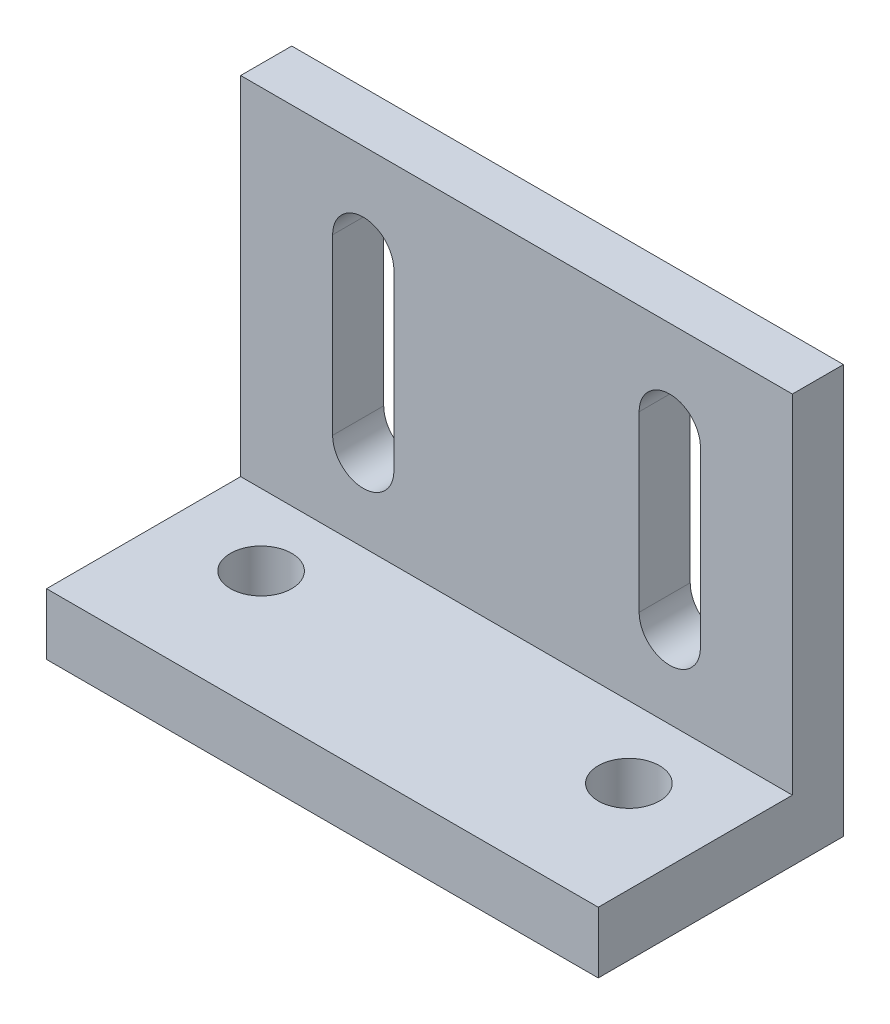
SolidWorks part; units mm, degrees
ref_plane "Front Plane" through (0, 0, 0) normal (0, 0, 1) x (1, 0, 0)
ref_plane "Top Plane" through (0, 0, 0) normal (0, 1, 0) x (1, 0, 0)
ref_plane "Right Plane" through (0, 0, 0) normal (1, 0, 0) x (0, 0, -1)
sketch "Sketch1" plane through (0, 0, 0) normal (1, 0, 0) x (0, 0, -1)
  line L0 (0, 0) -> (-12, 0)
  line L1 (-12, 0) -> (-12, 3)
  line L2 (-12, 3) -> (-2.5, 3)
  line L3 (-2.5, 3) -> (-2.5, 20)
  line L4 (-2.5, 20) -> (0, 20)
  line L5 (0, 20) -> (0, 0)
  dimension "D1" = 12
  dimension "D2" = 3
  dimension "D3" = 2.5
  dimension "D4" = 20
extrude "Boss-Extrude1" add sketch "Sketch1" along normal mid plane 27
sketch "Sketch2" plane through (0, 3, 0) normal (0, 1, 0) x (1, 0, 0)
  line L0 (-9, -6) -> (9, -6) construction
  line L1 (0, -6) -> (0, 0) construction
  circle A0 centre (-9, -6) radius 1.5
  circle A1 centre (9, -6) radius 1.5
  dimension "D2" = 3
  dimension "D1" = 18
  dimension "D3" = 6
extrude "Cut-Extrude1" cut sketch "Sketch2" against normal blind 20
sketch "Sketch3" plane through (0, 0, 2.5) normal (0, 0, 1) x (1, 0, 0)
  line L0 (-7.5, 15.5) -> (-7.5, 7) construction
  line L1 (-6.0005, 15.5) -> (-6.0005, 7)
  line L2 (-8.9995, 15.5) -> (-8.9995, 7)
  line L3 (7.5, 15.5) -> (7.5, 7) construction
  line L4 (8.9995, 15.5) -> (8.9995, 7)
  line L5 (6.0005, 15.5) -> (6.0005, 7)
  line L6 (-7.5, 11.25) -> (7.5, 11.25) construction
  line L7 (0, 11.25) -> (0, 0) construction
  line L8 (13.5, 0) -> (-13.5, 0) construction
  arc A0 (-6.0005, 15.5) -> (-8.9995, 15.5) centre (-7.5, 15.5) ccw
  arc A1 (-8.9995, 7) -> (-6.0005, 7) centre (-7.5, 7) ccw
  arc A2 (8.9995, 15.5) -> (6.0005, 15.5) centre (7.5, 15.5) ccw
  arc A3 (6.0005, 7) -> (8.9995, 7) centre (7.5, 7) ccw
  point P2 (-7.5, 11.25)
  point P7 (7.5, 11.25)
  dimension "D1" = 2.999
  dimension "D2" = 7
  dimension "D4" = 8.5
  dimension "D5" = 15
extrude "Cut-Extrude2" cut sketch "Sketch3" against normal through all
